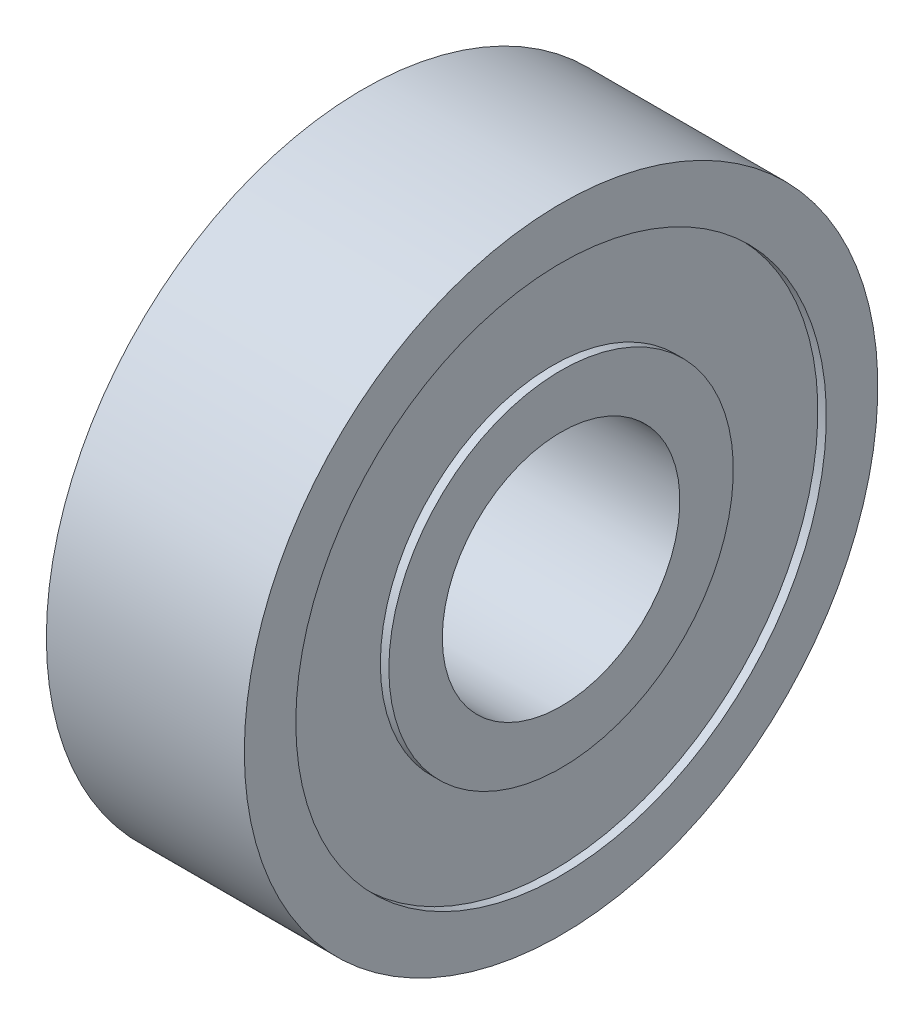
SolidWorks part; units mm, degrees
ref_plane "正面" through (0, 0, 0) normal (0, 0, 1) x (1, 0, 0)
ref_plane "平面" through (0, 0, 0) normal (0, 1, 0) x (1, 0, 0)
ref_plane "右側面" through (0, 0, 0) normal (1, 0, 0) x (0, 0, -1)
ref_plane "平面1" through (0, 0, 0) normal (0, 0, 1) x (1, 0, 0)
sketch "ｽｹｯﾁ1" plane through (0, 0, 0) normal (0, 0, 1) x (1, 0, 0)
  line L0 (0, 13.4) -> (0.43, 13.4)
  line L1 (0.43, 13.4) -> (0.43, 8.7)
  line L2 (0.43, 8.7) -> (0, 8.7)
  line L3 (0, 8.7) -> (0, 6)
  line L4 (0, 6) -> (10, 6)
  line L5 (10, 6) -> (10, 8.7)
  line L6 (10, 8.7) -> (9.57, 8.7)
  line L7 (9.57, 8.7) -> (9.57, 13.4)
  line L8 (9.57, 13.4) -> (10, 13.4)
  line L9 (10, 13.4) -> (10, 16)
  line L10 (10, 16) -> (0, 16)
  line L11 (0, 16) -> (0, 13.4)
  line L12 (50, 0) -> (-50, 0) construction
revolve "回転1" add sketch "ｽｹｯﾁ1" angle 360 about L12
